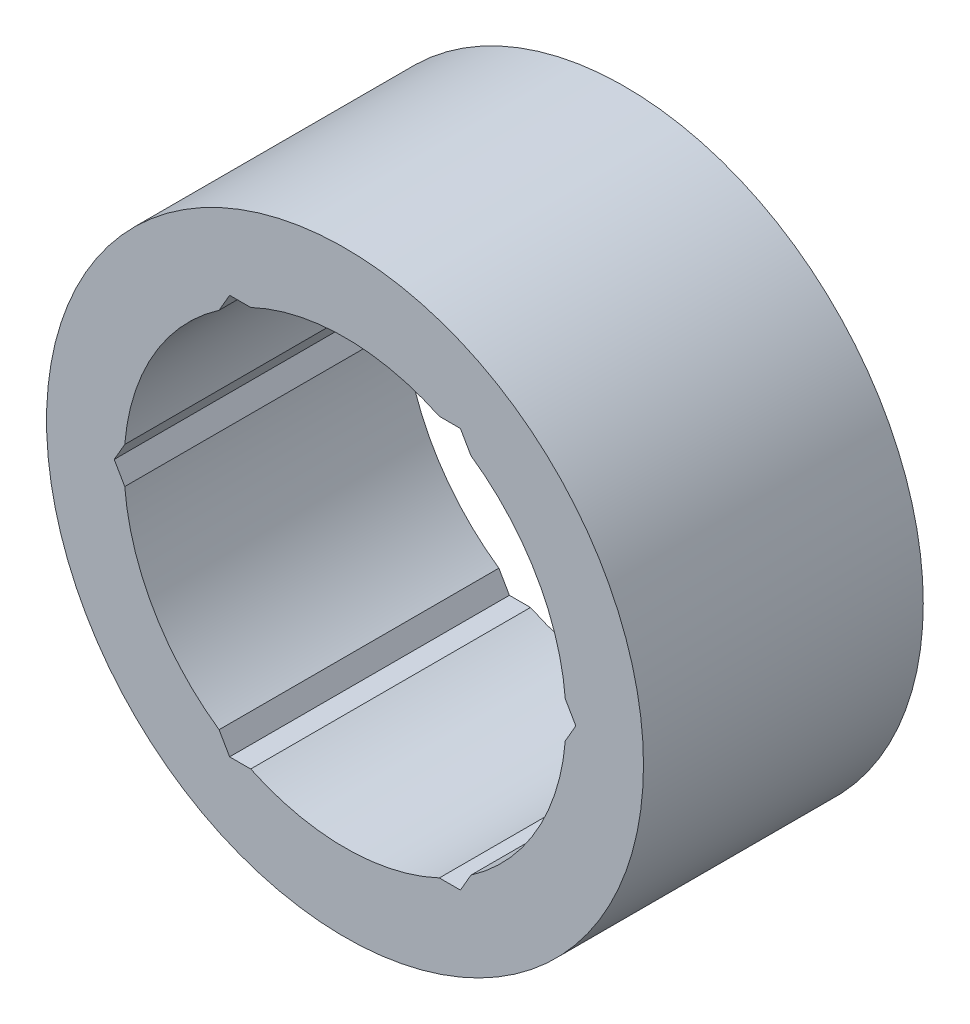
SolidWorks part; units mm, degrees
ref_plane "Front Plane" through (0, 0, 0) normal (0, 0, 1) x (1, 0, 0)
ref_plane "Top Plane" through (0, 0, 0) normal (0, 1, 0) x (1, 0, 0)
ref_plane "Right Plane" through (0, 0, 0) normal (1, 0, 0) x (0, 0, -1)
sketch "Sketch1" plane through (0, 0, 0) normal (0, 0, 1) x (1, 0, 0)
  circle A0 centre (0, 0) radius 10.668
  dimension "Pipe OD" = 21.336
extrude "Extrude-Thin1" add sketch "Sketch1" along normal mid plane 10 thin thin type one direction reverse wall 2.7686
sketch "Sketch3" plane through (0, 0, 5) normal (0, 0, 1) x (1, 0, 0)
  line L1 (4.1244, 7.1437) -> (-4.1244, 7.1437)
  line L2 (-4.1244, 7.1437) -> (-8.2489, 0)
  line L3 (-8.2489, 0) -> (-4.1244, -7.1438)
  line L4 (-4.1244, -7.1438) -> (4.1244, -7.1437)
  line L5 (4.1244, -7.1437) -> (8.2489, 0)
  line L6 (8.2489, 0) -> (4.1244, 7.1437)
  circle A0 centre (0, 0) radius 7.1438 construction
  dimension "D1" = 14.2875
extrude "Cut-Extrude3" cut sketch "Sketch3" against normal through all
